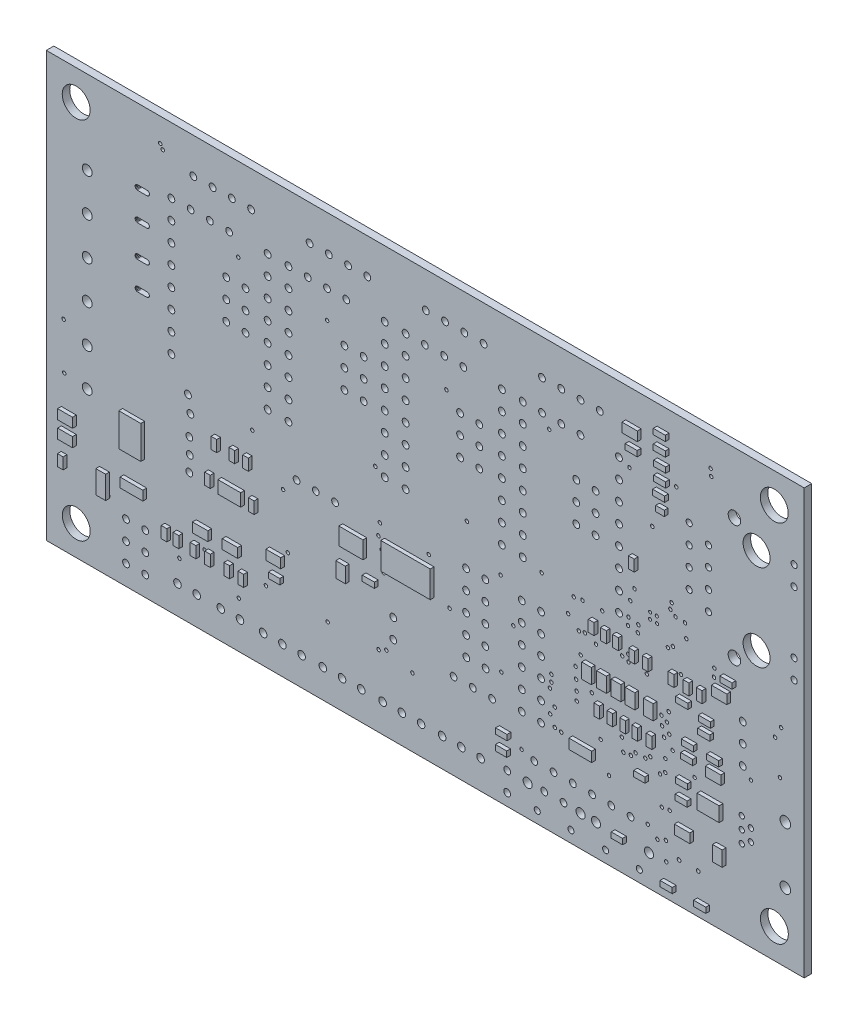
SolidWorks part; units mm, degrees
ref_plane "Front Plane" through (0, 0, 0) normal (0, 0, 1) x (1, 0, 0)
ref_plane "Top Plane" through (0, 0, 0) normal (0, 1, 0) x (1, 0, 0)
ref_plane "Right Plane" through (0, 0, 0) normal (1, 0, 0) x (0, 0, -1)
sketch "Sketch1" plane through (0, 0, 0) normal (0, 0, 1) x (1, 0, 0)
  line L0 (-23.2947, 26.1235) -> (-23.4059, 26.1039)
  line L1 (-23.4059, 26.1039) -> (-24.6559, 26.1039)
  line L2 (-24.6559, 26.1039) -> (-24.767, 26.1235)
  line L3 (-24.767, 26.1235) -> (-24.8648, 26.18)
  line L4 (-24.8648, 26.18) -> (-24.9373, 26.2664)
  line L5 (-24.9373, 26.2664) -> (-24.9759, 26.3725)
  line L6 (-24.9759, 26.3725) -> (-24.9759, 26.4854)
  line L7 (-24.9759, 26.4854) -> (-24.9373, 26.5914)
  line L8 (-24.9373, 26.5914) -> (-24.8648, 26.6779)
  line L9 (-24.8648, 26.6779) -> (-24.767, 26.7343)
  line L10 (-24.767, 26.7343) -> (-24.6559, 26.7539)
  line L11 (-24.6559, 26.7539) -> (-23.2947, 26.7343)
  line L12 (-23.2947, 26.7343) -> (-23.197, 26.6779)
  line L13 (-23.197, 26.6779) -> (-23.1244, 26.5914)
  line L14 (-23.1244, 26.5914) -> (-23.0858, 26.4854)
  line L15 (-23.0858, 26.4854) -> (-23.0858, 26.3725)
  line L16 (-23.0858, 26.3725) -> (-23.1244, 26.2664)
  line L17 (-23.1244, 26.2664) -> (-23.197, 26.18)
  line L18 (-23.197, 26.18) -> (-23.2947, 26.1235)
  line L19 (-23.2947, 29.8319) -> (-23.4059, 29.8123)
  line L20 (-23.4059, 29.8123) -> (-24.6559, 29.8123)
  line L21 (-24.6559, 29.8123) -> (-24.767, 29.8319)
  line L22 (-24.767, 29.8319) -> (-24.8648, 29.8884)
  line L23 (-24.8648, 29.8884) -> (-24.9373, 29.9748)
  line L24 (-24.9373, 29.9748) -> (-24.9759, 30.0809)
  line L25 (-24.9759, 30.0809) -> (-24.9759, 30.1938)
  line L26 (-24.9759, 30.1938) -> (-24.9373, 30.2998)
  line L27 (-24.9373, 30.2998) -> (-24.8648, 30.3863)
  line L28 (-24.8648, 30.3863) -> (-24.767, 30.4427)
  line L29 (-24.767, 30.4427) -> (-24.6559, 30.4623)
  line L30 (-24.6559, 30.4623) -> (-23.2947, 30.4427)
  line L31 (-23.2947, 30.4427) -> (-23.197, 30.3863)
  line L32 (-23.197, 30.3863) -> (-23.1244, 30.2998)
  line L33 (-23.1244, 30.2998) -> (-23.0858, 30.1938)
  line L34 (-23.0858, 30.1938) -> (-23.0858, 30.0809)
  line L35 (-23.0858, 30.0809) -> (-23.1244, 29.9748)
  line L36 (-23.1244, 29.9748) -> (-23.197, 29.8884)
  line L37 (-23.197, 29.8884) -> (-23.2947, 29.8319)
  line L38 (-23.2947, 34.0229) -> (-23.4059, 34.0033)
  line L39 (-23.4059, 34.0033) -> (-24.6559, 34.0033)
  line L40 (-24.6559, 34.0033) -> (-24.767, 34.0229)
  line L41 (-24.767, 34.0229) -> (-24.8648, 34.0794)
  line L42 (-24.8648, 34.0794) -> (-24.9373, 34.1658)
  line L43 (-24.9373, 34.1658) -> (-24.9759, 34.2719)
  line L44 (-24.9759, 34.2719) -> (-24.9759, 34.3848)
  line L45 (-24.9759, 34.3848) -> (-24.9373, 34.4908)
  line L46 (-24.9373, 34.4908) -> (-24.8648, 34.5773)
  line L47 (-24.8648, 34.5773) -> (-24.767, 34.6337)
  line L48 (-24.767, 34.6337) -> (-24.6559, 34.6533)
  line L49 (-24.6559, 34.6533) -> (-23.2947, 34.6337)
  line L50 (-23.2947, 34.6337) -> (-23.197, 34.5773)
  line L51 (-23.197, 34.5773) -> (-23.1244, 34.4908)
  line L52 (-23.1244, 34.4908) -> (-23.0858, 34.3848)
  line L53 (-23.0858, 34.3848) -> (-23.0858, 34.2719)
  line L54 (-23.0858, 34.2719) -> (-23.1244, 34.1658)
  line L55 (-23.1244, 34.1658) -> (-23.197, 34.0794)
  line L56 (-23.197, 34.0794) -> (-23.2947, 34.0229)
  line L57 (-23.2947, 37.7313) -> (-23.4059, 37.7117)
  line L58 (-23.4059, 37.7117) -> (-24.6559, 37.7117)
  line L59 (-24.6559, 37.7117) -> (-24.767, 37.7313)
  line L60 (-24.767, 37.7313) -> (-24.8648, 37.7878)
  line L61 (-24.8648, 37.7878) -> (-24.9373, 37.8742)
  line L62 (-24.9373, 37.8742) -> (-24.9759, 37.9803)
  line L63 (-24.9759, 37.9803) -> (-24.9759, 38.0932)
  line L64 (-24.9759, 38.0932) -> (-24.9373, 38.1992)
  line L65 (-24.9373, 38.1992) -> (-24.8648, 38.2857)
  line L66 (-24.8648, 38.2857) -> (-24.767, 38.3421)
  line L67 (-24.767, 38.3421) -> (-24.6559, 38.3617)
  line L68 (-24.6559, 38.3617) -> (-23.2947, 38.3421)
  line L69 (-23.2947, 38.3421) -> (-23.197, 38.2857)
  line L70 (-23.197, 38.2857) -> (-23.1244, 38.1992)
  line L71 (-23.1244, 38.1992) -> (-23.0858, 38.0932)
  line L72 (-23.0858, 38.0932) -> (-23.0858, 37.9803)
  line L73 (-23.0858, 37.9803) -> (-23.1244, 37.8742)
  line L74 (-23.1244, 37.8742) -> (-23.197, 37.7878)
  line L75 (-23.197, 37.7878) -> (-23.2947, 37.7313)
  line L76 (63.3071, -8.3113) -> (63.3071, 47.6887)
  line L77 (63.3071, 47.6887) -> (-36.6929, 47.6887)
  line L78 (-36.6929, 47.6887) -> (-36.6929, -8.3113)
  line L79 (-36.6929, -8.3113) -> (63.3071, -8.3113)
  circle A0 centre (16.5171, 10.5421) radius 0.2286
  circle A1 centre (16.1038, 35.2921) radius 0.2286
  circle A2 centre (23.2471, 17.7087) radius 0.2286
  circle A3 centre (28.655, 20.675) radius 0.2286
  circle A4 centre (33.2873, 8.324) radius 0.2286
  circle A5 centre (29.7584, 8.0388) radius 0.2286
  circle A6 centre (7.3249, 15.7176) radius 0.2286
  circle A7 centre (0.3571, 35.3487) radius 0.2286
  circle A8 centre (18.7985, 21.6213) radius 0.2286
  circle A9 centre (29.9537, 9.7164) radius 0.2286
  circle A10 centre (29.9571, 8.8187) radius 0.2286
  circle A11 centre (13.775, 15.3137) radius 0.2286
  circle A12 centre (-11.3662, 36.7154) radius 0.2286
  circle A13 centre (-9.5149, 17.8687) radius 0.2286
  circle A14 centre (31.2407, 3.7565) radius 0.2286
  circle A15 centre (23.3471, 6.6687) radius 0.2286
  circle A16 centre (-4.8229, 6.2254) radius 0.2286
  circle A17 centre (-5.4559, 13.1265) radius 0.2286
  circle A18 centre (44.2803, 5.4921) radius 0.2286
  circle A19 centre (44.978, 6.0054) radius 0.2286
  circle A20 centre (44.4754, 12.3113) radius 0.2286
  circle A21 centre (43.2671, 33.2787) radius 0.2286
  circle A22 centre (42.6598, -1.0665) radius 0.2286
  circle A23 centre (34.3671, 16.6587) radius 0.2286
  circle A24 centre (60.1092, 12.993) radius 0.2286
  circle A25 centre (34.0541, 20.2274) radius 0.2286
  circle A26 centre (32.8957, 20.0402) radius 0.2286
  circle A27 centre (59.4648, 17.2764) radius 0.2286
  circle A28 centre (35.8363, 16.1019) radius 0.2286
  circle A29 centre (45.058, -1.7073) radius 0.2286
  circle A30 centre (45.196, 11.8765) radius 0.2286
  circle A31 centre (45.4971, 10.6387) radius 0.2286
  circle A32 centre (47.5771, 24.4066) radius 0.2286
  circle A33 centre (45.9424, 9.0166) radius 0.2286
  circle A34 centre (7.1314, 14.1277) radius 0.2286
  circle A35 centre (8.1788, 1.5814) radius 0.2286
  circle A36 centre (7.1505, 1.1324) radius 0.2286
  circle A37 centre (7.5602, 12.7235) radius 0.2286
  circle A38 centre (33.5707, 16.4904) radius 0.2286
  circle A39 centre (30.4055, 3.869) radius 0.2286
  circle A40 centre (33.8171, 13.8587) radius 0.2286
  circle A41 centre (45.5541, 1.9605) radius 0.2286
  circle A42 centre (44.5228, 1.8236) radius 0.2286
  circle A43 centre (29.78, 5.116) radius 0.2286
  circle A44 centre (35.2805, 10.2754) radius 0.2286
  circle A45 centre (33.1373, 12.2162) radius 0.2286
  circle A46 centre (24.9359, 12.76) radius 0.2286
  circle A47 centre (44.9896, 7.609) radius 0.2286
  circle A48 centre (36.4471, 5.5187) radius 0.2286
  circle A49 centre (48.8405, 7.3754) radius 0.2286
  circle A50 centre (39.4484, 5.5491) radius 0.2286
  circle A51 centre (40.4371, 5.6921) radius 0.2286
  circle A52 centre (33.2744, 9.4587) radius 0.2286
  circle A53 centre (33.2072, 10.7806) radius 0.2286
  circle A54 centre (-19.1295, -1.5746) radius 0.2286
  circle A55 centre (45.4266, 13.1794) radius 0.2286
  circle A56 centre (11.6171, 0.7045) radius 0.2286
  circle A57 centre (41.4271, 21.1092) radius 0.2286
  circle A58 centre (47.7471, 22.6787) radius 0.2286
  circle A59 centre (40.9171, 24.9787) radius 0.2286
  circle A60 centre (41.361, 20.1656) radius 0.2286
  circle A61 centre (46.4271, 39.3687) radius 0.2286
  circle A62 centre (40.2556, 38.4838) radius 0.2286
  circle A63 centre (40.3571, 23.3387) radius 0.2286
  circle A64 centre (41.0541, 6.2989) radius 0.2286
  circle A65 centre (39.2531, 7.1827) radius 0.2286
  circle A66 centre (42.3388, 6.3287) radius 0.2286
  circle A67 centre (42.9945, 6.828) radius 0.2286
  circle A68 centre (30.3864, 6.1865) radius 0.2286
  circle A69 centre (-34.4069, 18.1115) radius 0.2286
  circle A70 centre (-28.5043, 0.9409) radius 0.2286
  circle A71 centre (26.0116, -0.8344) radius 0.2286
  circle A72 centre (7.8107, 10.2366) radius 0.2286
  circle A73 centre (29.6671, 37.5587) radius 0.2286
  circle A74 centre (45.6571, 24.9887) radius 0.2286
  circle A75 centre (46.3271, 24.4887) radius 0.2286
  circle A76 centre (45.8071, 25.8287) radius 0.2286
  circle A77 centre (40.0912, 17.0729) radius 0.2286
  circle A78 centre (40.1231, 16.2051) radius 0.2286
  circle A79 centre (40.1205, 21.3421) radius 0.2286
  circle A80 centre (47.0471, 18.2387) radius 0.2286
  circle A81 centre (51.4538, 21.1754) radius 0.2286
  circle A82 centre (40.0605, 20.3421) radius 0.2286
  circle A83 centre (36.6571, 20.3187) radius 0.2286
  circle A84 centre (45.3255, 20.4579) radius 0.2286
  circle A85 centre (39.2971, 16.4887) radius 0.2286
  circle A86 centre (45.9871, 20.9187) radius 0.2286
  circle A87 centre (42.5415, 16.037) radius 0.2286
  circle A88 centre (-11.2929, -2.2113) radius 0.2286
  circle A89 centre (32.1571, 17.7487) radius 0.2286
  circle A90 centre (-15.7962, 1.0487) radius 0.2286
  circle A91 centre (45.1071, -4.1313) radius 0.2286
  circle A92 centre (44.8148, 9.9587) radius 0.2286
  circle A93 centre (0.4297, 0.9345) radius 0.2286
  circle A94 centre (43.9401, -2.1493) radius 0.2286
  circle A95 centre (51.4038, 20.1054) radius 0.2286
  circle A96 centre (56.2838, 10.7887) radius 0.2286
  circle A97 centre (60.2524, 18.7787) radius 0.2286
  circle A98 centre (44.5511, 11.1298) radius 0.2286
  circle A99 centre (-7.7129, 1.0087) radius 0.2286
  circle A100 centre (6.7171, 21.8554) radius 0.2286
  circle A101 centre (37.5541, 1.9585) radius 0.2286
  circle A102 centre (51.046, 42.8634) radius 0.2286
  circle A103 centre (50.9547, 43.7429) radius 0.2286
  circle A104 centre (-21.327, 44.0122) radius 0.2286
  circle A105 centre (-21.6644, 44.556) radius 0.2286
  circle A106 centre (-34.3297, 12.0029) radius 0.2286
  circle A107 centre (-9.6695, 43.0214) radius 0.45
  circle A108 centre (-12.2095, 43.0214) radius 0.45
  circle A109 centre (-14.7495, 43.0167) radius 0.45
  circle A110 centre (-17.2895, 43.0121) radius 0.45
  circle A111 centre (5.6671, 43.0314) radius 0.45
  circle A112 centre (3.1271, 43.0314) radius 0.45
  circle A113 centre (0.5871, 43.0267) radius 0.45
  circle A114 centre (-1.9529, 43.0221) radius 0.45
  circle A115 centre (21.0038, 43.0214) radius 0.45
  circle A116 centre (18.4638, 43.0214) radius 0.45
  circle A117 centre (15.9238, 43.0167) radius 0.45
  circle A118 centre (13.3838, 43.0121) radius 0.45
  circle A119 centre (36.3338, 43.0014) radius 0.45
  circle A120 centre (33.7938, 43.0014) radius 0.45
  circle A121 centre (31.2538, 42.9967) radius 0.45
  circle A122 centre (28.7138, 42.9921) radius 0.45
  circle A123 centre (42.9771, 22.5087) radius 0.2032
  circle A124 centre (43.8889, 22.474) radius 0.2032
  circle A125 centre (43.8541, 23.3249) radius 0.2032
  circle A126 centre (42.9858, 23.3249) radius 0.2032
  circle A127 centre (32.5312, -6.7873) radius 0.4
  circle A128 centre (28.0862, -6.7873) radius 0.4
  circle A129 centre (33.8012, -4.2473) radius 0.6
  circle A130 centre (26.8162, -4.2473) radius 0.6
  circle A131 centre (57.0241, 37.3877) radius 1.778
  circle A132 centre (57.0241, 25.9577) radius 1.778
  circle A133 centre (61.9771, 35.7367) radius 0.4064
  circle A134 centre (61.9771, 38.2767) radius 0.4064
  circle A135 centre (48.1341, 28.4977) radius 0.4064
  circle A136 centre (50.6741, 27.2277) radius 0.4064
  circle A137 centre (54.1031, 23.6717) radius 0.8255
  circle A138 centre (54.1031, 39.6737) radius 0.8255
  circle A139 centre (48.1341, 33.5777) radius 0.4064
  circle A140 centre (50.6741, 29.7677) radius 0.4064
  circle A141 centre (50.6741, 32.3077) radius 0.4064
  circle A142 centre (48.1341, 31.0377) radius 0.4064
  circle A143 centre (50.6741, 34.8477) radius 0.4064
  circle A144 centre (48.1341, 36.1177) radius 0.4064
  circle A145 centre (61.9771, 27.6087) radius 0.4064
  circle A146 centre (61.9771, 25.0687) radius 0.4064
  circle A147 centre (9.0886, 3.245) radius 0.4445
  circle A148 centre (9.0886, 5.785) radius 0.4445
  circle A149 centre (21.2699, 6.0397) radius 0.4445
  circle A150 centre (18.7299, 6.0397) radius 0.4445
  circle A151 centre (41.5524, -6.7788) radius 0.4
  circle A152 centre (37.1074, -6.7788) radius 0.4
  circle A153 centre (42.8224, -4.2388) radius 0.6
  circle A154 centre (35.8374, -4.2388) radius 0.6
  circle A155 centre (59.3696, -4.3808) radius 1.8415
  circle A156 centre (59.3604, 43.7422) radius 1.8415
  circle A157 centre (-32.7488, 43.7345) radius 1.8415
  circle A158 centre (-32.7404, -4.3748) radius 1.8415
  circle A159 centre (-17.8195, 12.9654) radius 0.45
  circle A160 centre (-17.8184, 8.8932) radius 0.45
  circle A161 centre (-17.7629, 10.9287) radius 0.45
  circle A162 centre (-17.6821, 15.653) radius 0.45
  circle A163 centre (-18.0029, 17.7187) radius 0.45
  circle A164 centre (33.7912, 38.9854) radius 0.4445
  circle A165 centre (31.2512, 38.9854) radius 0.4445
  circle A166 centre (28.7112, 38.9854) radius 0.4445
  circle A167 centre (26.1712, 21.2054) radius 0.45
  circle A168 centre (26.1712, 36.4454) radius 0.45
  circle A169 centre (38.8712, 36.4454) radius 0.45
  circle A170 centre (38.8712, 33.9054) radius 0.45
  circle A171 centre (38.8712, 31.3654) radius 0.45
  circle A172 centre (38.8712, 28.8254) radius 0.45
  circle A173 centre (38.8712, 26.2854) radius 0.45
  circle A174 centre (38.8712, 23.7454) radius 0.45
  circle A175 centre (26.1712, 23.7454) radius 0.45
  circle A176 centre (26.1712, 38.9854) radius 0.45
  circle A177 centre (38.8712, 21.2054) radius 0.45
  circle A178 centre (38.8712, 38.9854) radius 0.45
  circle A179 centre (26.1712, 26.2854) radius 0.45
  circle A180 centre (26.1712, 28.8254) radius 0.45
  circle A181 centre (26.1712, 33.9054) radius 0.45
  circle A182 centre (26.1712, 31.3654) radius 0.45
  circle A183 centre (18.3371, 39.0254) radius 0.4445
  circle A184 centre (15.7971, 39.0254) radius 0.4445
  circle A185 centre (13.2571, 39.0254) radius 0.4445
  circle A186 centre (10.7171, 21.2454) radius 0.45
  circle A187 centre (10.7171, 36.4854) radius 0.45
  circle A188 centre (23.4171, 36.4854) radius 0.45
  circle A189 centre (23.4171, 33.9454) radius 0.45
  circle A190 centre (23.4171, 31.4054) radius 0.45
  circle A191 centre (23.4171, 28.8654) radius 0.45
  circle A192 centre (23.4171, 26.3254) radius 0.45
  circle A193 centre (23.4171, 23.7854) radius 0.45
  circle A194 centre (10.7171, 23.7854) radius 0.45
  circle A195 centre (10.7171, 39.0254) radius 0.45
  circle A196 centre (23.4171, 21.2454) radius 0.45
  circle A197 centre (23.4171, 39.0254) radius 0.45
  circle A198 centre (10.7171, 26.3254) radius 0.45
  circle A199 centre (10.7171, 28.8654) radius 0.45
  circle A200 centre (10.7171, 33.9454) radius 0.45
  circle A201 centre (10.7171, 31.4054) radius 0.45
  circle A202 centre (2.8838, 39.0154) radius 0.4445
  circle A203 centre (0.3438, 39.0154) radius 0.4445
  circle A204 centre (-2.1962, 39.0154) radius 0.4445
  circle A205 centre (-4.7362, 21.2354) radius 0.45
  circle A206 centre (-4.7362, 36.4754) radius 0.45
  circle A207 centre (7.9638, 36.4754) radius 0.45
  circle A208 centre (7.9638, 33.9354) radius 0.45
  circle A209 centre (7.9638, 31.3954) radius 0.45
  circle A210 centre (7.9638, 28.8554) radius 0.45
  circle A211 centre (7.9638, 26.3154) radius 0.45
  circle A212 centre (7.9638, 23.7754) radius 0.45
  circle A213 centre (-4.7362, 23.7754) radius 0.45
  circle A214 centre (-4.7362, 39.0154) radius 0.45
  circle A215 centre (7.9638, 21.2354) radius 0.45
  circle A216 centre (7.9638, 39.0154) radius 0.45
  circle A217 centre (-4.7362, 26.3154) radius 0.45
  circle A218 centre (-4.7362, 28.8554) radius 0.45
  circle A219 centre (-4.7362, 33.9354) radius 0.45
  circle A220 centre (-4.7362, 31.3954) radius 0.45
  circle A221 centre (-12.5695, 39.0254) radius 0.4445
  circle A222 centre (-15.1095, 39.0254) radius 0.4445
  circle A223 centre (-17.6495, 39.0254) radius 0.4445
  circle A224 centre (-20.1895, 21.2454) radius 0.45
  circle A225 centre (-20.1895, 36.4854) radius 0.45
  circle A226 centre (-7.4895, 36.4854) radius 0.45
  circle A227 centre (-7.4895, 33.9454) radius 0.45
  circle A228 centre (-7.4895, 31.4054) radius 0.45
  circle A229 centre (-7.4895, 28.8654) radius 0.45
  circle A230 centre (-7.4895, 26.3254) radius 0.45
  circle A231 centre (-7.4895, 23.7854) radius 0.45
  circle A232 centre (-20.1895, 23.7854) radius 0.45
  circle A233 centre (-20.1895, 39.0254) radius 0.45
  circle A234 centre (-7.4895, 21.2454) radius 0.45
  circle A235 centre (-7.4895, 39.0254) radius 0.45
  circle A236 centre (-20.1895, 26.3254) radius 0.45
  circle A237 centre (-20.1895, 28.8654) radius 0.45
  circle A238 centre (-20.1895, 33.9454) radius 0.45
  circle A239 centre (-20.1895, 31.4054) radius 0.45
  circle A240 centre (55.1971, 16.9454) radius 0.4445
  circle A241 centre (55.1971, 14.4054) radius 0.4445
  circle A242 centre (55.1971, 11.8654) radius 0.4445
  circle A243 centre (-13.6768, -4.5792) radius 0.5
  circle A244 centre (-11.1368, -4.5745) radius 0.5
  circle A245 centre (-19.3847, -4.5792) radius 0.5
  circle A246 centre (-16.8447, -4.5745) radius 0.5
  circle A247 centre (-3.6729, 15.0986) radius 0.4445
  circle A248 centre (-1.1329, 15.0986) radius 0.4445
  circle A249 centre (1.4071, 15.0986) radius 0.4445
  circle A250 centre (22.1258, 3.0017) radius 0.4445
  circle A251 centre (19.5858, 3.0017) radius 0.4445
  circle A252 centre (17.0458, 3.0017) radius 0.4445
  circle A253 centre (15.5317, -4.5494) radius 0.5
  circle A254 centre (18.0717, -4.5448) radius 0.5
  circle A255 centre (20.6117, -4.5401) radius 0.5
  circle A256 centre (7.6781, -4.5494) radius 0.5
  circle A257 centre (10.2181, -4.5448) radius 0.5
  circle A258 centre (12.7581, -4.5401) radius 0.5
  circle A259 centre (-0.2119, -4.5494) radius 0.5
  circle A260 centre (2.3281, -4.5448) radius 0.5
  circle A261 centre (4.8681, -4.5401) radius 0.5
  circle A262 centre (-8.0837, -4.5858) radius 0.5
  circle A263 centre (-5.5437, -4.5812) radius 0.5
  circle A264 centre (-3.0037, -4.5765) radius 0.5
  circle A265 centre (-12.9462, 28.5621) radius 0.4445
  circle A266 centre (-12.9462, 31.1021) radius 0.4445
  circle A267 centre (-12.9462, 33.6421) radius 0.4445
  circle A268 centre (-10.4062, 28.5621) radius 0.4445
  circle A269 centre (-10.4062, 31.1021) radius 0.4445
  circle A270 centre (-10.4062, 33.6421) radius 0.4445
  circle A271 centre (2.6405, 28.5454) radius 0.4445
  circle A272 centre (2.6405, 31.0854) radius 0.4445
  circle A273 centre (2.6405, 33.6254) radius 0.4445
  circle A274 centre (5.1805, 28.5454) radius 0.4445
  circle A275 centre (5.1805, 31.0854) radius 0.4445
  circle A276 centre (5.1805, 33.6254) radius 0.4445
  circle A277 centre (17.8997, 28.4679) radius 0.4445
  circle A278 centre (17.8997, 31.0079) radius 0.4445
  circle A279 centre (17.8997, 33.5479) radius 0.4445
  circle A280 centre (20.4397, 28.4679) radius 0.4445
  circle A281 centre (20.4397, 31.0079) radius 0.4445
  circle A282 centre (20.4397, 33.5479) radius 0.4445
  circle A283 centre (33.2389, 28.5087) radius 0.4445
  circle A284 centre (33.2389, 31.0487) radius 0.4445
  circle A285 centre (33.2389, 33.5887) radius 0.4445
  circle A286 centre (35.7789, 28.5087) radius 0.4445
  circle A287 centre (35.7789, 31.0487) radius 0.4445
  circle A288 centre (35.7789, 33.5887) radius 0.4445
  circle A289 centre (24.1205, -6.7339) radius 0.4445
  circle A290 centre (24.1205, -4.1939) radius 0.4445
  circle A291 centre (27.6961, -1.3263) radius 0.4445
  circle A292 centre (30.2361, -1.3263) radius 0.4445
  circle A293 centre (32.7761, -1.3263) radius 0.4445
  circle A294 centre (35.3161, -1.3263) radius 0.4445
  circle A295 centre (37.8561, -1.3263) radius 0.4445
  circle A296 centre (40.3961, -1.3263) radius 0.4445
  circle A297 centre (-31.2929, 11.6887) radius 0.65
  circle A298 centre (-31.2929, 16.6887) radius 0.65
  circle A299 centre (-31.2929, 21.6887) radius 0.65
  circle A300 centre (-31.2929, 26.6887) radius 0.65
  circle A301 centre (-31.2929, 31.6887) radius 0.65
  circle A302 centre (-31.2929, 36.6887) radius 0.65
  circle A303 centre (60.8153, 8.2611) radius 0.7
  circle A304 centre (60.8153, 0.7564) radius 0.7
  circle A305 centre (56.2671, 5.3087) radius 0.35
  circle A306 centre (56.2671, 3.7087) radius 0.35
  circle A307 centre (55.0671, 6.1087) radius 0.35
  circle A308 centre (55.0671, 2.9087) radius 0.35
  circle A309 centre (55.0671, 4.5087) radius 0.35
  circle A310 centre (28.5851, 16.1997) radius 0.4445
  circle A311 centre (28.5851, 13.6597) radius 0.4445
  circle A312 centre (28.5851, 11.1197) radius 0.4445
  circle A313 centre (26.0451, 16.1997) radius 0.4445
  circle A314 centre (26.0451, 13.6597) radius 0.4445
  circle A315 centre (26.0451, 11.1197) radius 0.4445
  circle A316 centre (-23.6384, -0.6061) radius 0.4445
  circle A317 centre (-23.6384, -3.1461) radius 0.4445
  circle A318 centre (-23.6384, -5.6861) radius 0.4445
  circle A319 centre (-26.1784, -0.6061) radius 0.4445
  circle A320 centre (-26.1784, -3.1461) radius 0.4445
  circle A321 centre (-26.1784, -5.6861) radius 0.4445
  circle A322 centre (28.5851, 8.5797) radius 0.4445
  circle A323 centre (28.5851, 6.0397) radius 0.4445
  circle A324 centre (28.5851, 3.4997) radius 0.4445
  circle A325 centre (26.0451, 8.5797) radius 0.4445
  circle A326 centre (26.0451, 6.0397) radius 0.4445
  circle A327 centre (26.0451, 3.4997) radius 0.4445
  circle A328 centre (18.6949, 11.1179) radius 0.4445
  circle A329 centre (18.6949, 13.6579) radius 0.4445
  circle A330 centre (18.6949, 16.1979) radius 0.4445
  circle A331 centre (21.2349, 11.1179) radius 0.4445
  circle A332 centre (21.2349, 13.6579) radius 0.4445
  circle A333 centre (21.2349, 16.1979) radius 0.4445
  circle A334 centre (21.2349, 8.5779) radius 0.4445
  circle A335 centre (18.6949, 8.5779) radius 0.4445
  circle A336 centre (31.5511, -4.1456) radius 0.4445
  circle A337 centre (29.0111, -4.1456) radius 0.4445
  circle A338 centre (46.796, -3.0784) radius 0.25
  circle A339 centre (49.3193, -3.0803) radius 0.25
extrude "Boss-Extrude1" add sketch "Sketch1" against normal blind 0.991
sketch "Sketch2" plane through (0, 0, 0) normal (0, 0, 1) x (1, 0, 0)
  line L0 (-32.7488, 43.7345) -> (59.3696, -4.3808) construction
  line L1 (-32.7404, -4.3748) -> (59.3604, 43.7422) construction
  line L2 (-24.0309, 26.1039) -> (-23.9753, 30.4525) construction
  line L3 (-24.6559, 26.1039) -> (-23.4059, 26.1039) construction
  line L4 (-23.2947, 30.4427) -> (-24.6559, 30.4623) construction
  line L5 (-24.0309, 34.0033) -> (-23.9753, 38.3519) construction
  line L6 (-24.6559, 34.0033) -> (-23.4059, 34.0033) construction
  line L7 (-23.2947, 38.3421) -> (-24.6559, 38.3617) construction
  point P8 (13.3104, 19.6769)
sketch "Sketch3" plane through (0, 0, -0.991) normal (0, 0, -1) x (-1, 0, 0)
  line L0 (36.6929, -8.3113) -> (-63.3071, -8.3113) construction
  line L1 (-32.5371, 3.9387) -> (-46.5671, 3.9387)
  line L2 (-32.5371, 3.9387) -> (-32.5371, 17.9687)
  line L3 (-32.5371, 17.9687) -> (-46.5671, 17.9687)
  line L4 (-46.5671, 3.9387) -> (-46.5671, 17.9687)
  line L5 (-63.3071, -8.3113) -> (-63.3071, 47.6887) construction
  dimension "D1" = 12.25
  dimension "D2" = 16.74
  dimension "D3" = 14.03
extrude "Boss-Extrude2" add sketch "Sketch3" along normal blind 1.61
chamfer "Chamfer1" distance 0.61 angle 45 4 edges at (32.5371, 3.9387, -1.796) (32.5371, 17.9687, -1.796) (46.5671, 17.9687, -1.796) (46.5671, 3.9387, -1.796)
chamfer "Chamfer2" distance 0.61 angle 45 8 edges at (46.2621, 4.2437, -2.601) (46.5671, 10.9537, -2.601) (46.2621, 17.6637, -2.601) (39.5521, 17.9687, -2.601) (32.8421, 17.6637, -2.601) (32.5371, 10.9537, -2.601) (32.8421, 4.2437, -2.601) (39.5521, 3.9387, -2.601)
sketch "Sketch4" plane through (0, 0, 0) normal (0, 0, 1) x (1, 0, 0)
  line B0 (-36.6929, 47.6887) -> (-36.6929, -8.3113) construction
  line B1 (-36.6929, -8.3113) -> (63.3071, -8.3113) construction
  line B2 (63.3071, 47.6887) -> (-36.6929, 47.6887) construction
  line B3 (63.3071, -8.3113) -> (63.3071, 47.6887) construction
  line B4 (-29.6656, 3.6663) -> (-28.3606, 3.6663)
  line B5 (-28.3606, 3.6663) -> (-28.3606, 0.6544)
  line B6 (-28.3606, 0.6544) -> (-29.6656, 0.6544)
  line B7 (-29.6656, 0.6544) -> (-29.6656, 3.6663)
  line B8 (-34.7169, 1.3554) -> (-33.9692, 1.3554)
  line B9 (-33.9692, 1.3554) -> (-33.9692, 2.8489)
  line B10 (-33.9692, 2.8489) -> (-34.7169, 2.8489)
  line B11 (-34.7169, 2.8489) -> (-34.7169, 1.3554)
  line B12 (-34.7033, 4.5002) -> (-32.7358, 4.5002)
  line B13 (-32.7358, 4.5002) -> (-32.7358, 5.7752)
  line B14 (-32.7358, 5.7752) -> (-34.7033, 5.7752)
  line B15 (-34.7033, 5.7752) -> (-34.7033, 4.5002)
  line B16 (-34.7033, 6.7189) -> (-32.7358, 6.7189)
  line B17 (-32.7358, 6.7189) -> (-32.7358, 7.9939)
  line B18 (-32.7358, 7.9939) -> (-34.7033, 7.9939)
  line B19 (-34.7033, 7.9939) -> (-34.7033, 6.7189)
  line B20 (-26.465, 3.0514) -> (-23.4532, 3.0514)
  line B21 (-23.4532, 3.0514) -> (-23.4532, 4.2981)
  line B22 (-23.4532, 4.2981) -> (-26.465, 4.2981)
  line B23 (-26.465, 4.2981) -> (-26.465, 3.0514)
  line B24 (-21.0347, -0.0306) -> (-20.287, -0.0306)
  line B25 (-20.287, -0.0306) -> (-20.287, 1.4811)
  line B26 (-20.287, 1.4811) -> (-21.0347, 1.4811)
  line B27 (-21.0347, 1.4811) -> (-21.0347, -0.0306)
  line B28 (-19.462, -0.0273) -> (-18.7144, -0.0273)
  line B29 (-18.7144, -0.0273) -> (-18.7144, 1.4845)
  line B30 (-18.7144, 1.4845) -> (-19.462, 1.4845)
  line B31 (-19.462, 1.4845) -> (-19.462, -0.0273)
  line B32 (-17.2087, -0.0539) -> (-16.461, -0.0539)
  line B33 (-16.461, -0.0539) -> (-16.461, 1.4578)
  line B34 (-16.461, 1.4578) -> (-17.2087, 1.4578)
  line B35 (-17.2087, 1.4578) -> (-17.2087, -0.0539)
  line B36 (-15.3047, -0.0887) -> (-14.557, -0.0887)
  line B37 (-14.557, -0.0887) -> (-14.557, 1.423)
  line B38 (-14.557, 1.423) -> (-15.3047, 1.423)
  line B39 (-15.3047, 1.423) -> (-15.3047, -0.0887)
  line B40 (-12.7587, -0.1173) -> (-12.011, -0.1173)
  line B41 (-12.011, -0.1173) -> (-12.011, 1.3945)
  line B42 (-12.011, 1.3945) -> (-12.7587, 1.3945)
  line B43 (-12.7587, 1.3945) -> (-12.7587, -0.1173)
  line B44 (-10.9054, -0.1821) -> (-10.1577, -0.1821)
  line B45 (-10.1577, -0.1821) -> (-10.1577, 1.3297)
  line B46 (-10.1577, 1.3297) -> (-10.9054, 1.3297)
  line B47 (-10.9054, 1.3297) -> (-10.9054, -0.1821)
  line B48 (-15.308, 8.932) -> (-14.5604, 8.932)
  line B49 (-14.5604, 8.932) -> (-14.5604, 10.4437)
  line B50 (-14.5604, 10.4437) -> (-15.308, 10.4437)
  line B51 (-15.308, 10.4437) -> (-15.308, 8.932)
  line B52 (-14.458, 13.4458) -> (-13.7104, 13.4458)
  line B53 (-13.7104, 13.4458) -> (-13.7104, 14.9575)
  line B54 (-13.7104, 14.9575) -> (-14.458, 14.9575)
  line B55 (-14.458, 14.9575) -> (-14.458, 13.4458)
  line B56 (-12.0847, 13.3663) -> (-11.337, 13.3663)
  line B57 (-11.337, 13.3663) -> (-11.337, 14.8781)
  line B58 (-11.337, 14.8781) -> (-12.0847, 14.8781)
  line B59 (-12.0847, 14.8781) -> (-12.0847, 13.3663)
  line B60 (-10.2854, 13.4111) -> (-9.5377, 13.4111)
  line B61 (-9.5377, 13.4111) -> (-9.5377, 14.9229)
  line B62 (-9.5377, 14.9229) -> (-10.2854, 14.9229)
  line B63 (-10.2854, 14.9229) -> (-10.2854, 13.4111)
  line B64 (36.0513, 8.2411) -> (36.799, 8.2411)
  line B65 (36.799, 8.2411) -> (36.799, 9.7529)
  line B66 (36.799, 9.7529) -> (36.0513, 9.7529)
  line B67 (36.0513, 9.7529) -> (36.0513, 8.2411)
  line B68 (37.7825, 8.2395) -> (38.5301, 8.2395)
  line B69 (38.5301, 8.2395) -> (38.5301, 9.7513)
  line B70 (38.5301, 9.7513) -> (37.7825, 9.7513)
  line B71 (37.7825, 9.7513) -> (37.7825, 8.2395)
  line B72 (39.4746, 8.2627) -> (40.2223, 8.2627)
  line B73 (40.2223, 8.2627) -> (40.2223, 9.7745)
  line B74 (40.2223, 9.7745) -> (39.4746, 9.7745)
  line B75 (39.4746, 9.7745) -> (39.4746, 8.2627)
  line B76 (41.0758, 8.2345) -> (41.8235, 8.2345)
  line B77 (41.8235, 8.2345) -> (41.8235, 9.7462)
  line B78 (41.8235, 9.7462) -> (41.0758, 9.7462)
  line B79 (41.0758, 9.7462) -> (41.0758, 8.2345)
  line B80 (35.3119, 18.9297) -> (36.0769, 18.9297)
  line B81 (36.0769, 18.9297) -> (36.0769, 17.4362)
  line B82 (36.0769, 17.4362) -> (35.3119, 17.4362)
  line B83 (35.3119, 17.4362) -> (35.3119, 18.9297)
  line B84 (36.9268, 18.8025) -> (37.6918, 18.8025)
  line B85 (37.6918, 18.8025) -> (37.6918, 17.3091)
  line B86 (37.6918, 17.3091) -> (36.9268, 17.3091)
  line B87 (36.9268, 17.3091) -> (36.9268, 18.8025)
  line B88 (38.5268, 18.8125) -> (39.2918, 18.8125)
  line B89 (39.2918, 18.8125) -> (39.2918, 17.3191)
  line B90 (39.2918, 17.3191) -> (38.5268, 17.3191)
  line B91 (38.5268, 17.3191) -> (38.5268, 18.8125)
  line B92 (40.6746, 18.3551) -> (41.4396, 18.3551)
  line B93 (41.4396, 18.3551) -> (41.4396, 16.8616)
  line B94 (41.4396, 16.8616) -> (40.6746, 16.8616)
  line B95 (40.6746, 16.8616) -> (40.6746, 18.3551)
  line B96 (42.4546, 18.3651) -> (43.2196, 18.3651)
  line B97 (43.2196, 18.3651) -> (43.2196, 16.8716)
  line B98 (43.2196, 16.8716) -> (42.4546, 16.8716)
  line B99 (42.4546, 16.8716) -> (42.4546, 18.3651)
  line B100 (40.6168, 28.8454) -> (41.3818, 28.8454)
  line B101 (41.3818, 28.8454) -> (41.3818, 27.3519)
  line B102 (41.3818, 27.3519) -> (40.6168, 27.3519)
  line B103 (40.6168, 27.3519) -> (40.6168, 28.8454)
  line B104 (45.8568, 18.2668) -> (46.6218, 18.2668)
  line B105 (46.6218, 18.2668) -> (46.6218, 16.7733)
  line B106 (46.6218, 16.7733) -> (45.8568, 16.7733)
  line B107 (45.8568, 16.7733) -> (45.8568, 18.2668)
  line B108 (47.8318, 18.2968) -> (48.5968, 18.2968)
  line B109 (48.5968, 18.2968) -> (48.5968, 16.8033)
  line B110 (48.5968, 16.8033) -> (47.8318, 16.8033)
  line B111 (47.8318, 16.8033) -> (47.8318, 18.2968)
  line B112 (49.5646, 18.2751) -> (50.3296, 18.2751)
  line B113 (50.3296, 18.2751) -> (50.3296, 16.7816)
  line B114 (50.3296, 16.7816) -> (49.5646, 16.7816)
  line B115 (49.5646, 16.7816) -> (49.5646, 18.2751)
  line B116 (-16.9162, 2.6968) -> (-14.8762, 2.6968)
  line B117 (-14.8762, 2.6968) -> (-14.8762, 3.9433)
  line B118 (-14.8762, 3.9433) -> (-16.9162, 3.9433)
  line B119 (-16.9162, 3.9433) -> (-16.9162, 2.6968)
  line B120 (-12.9795, 2.7523) -> (-10.9395, 2.7523)
  line B121 (-10.9395, 2.7523) -> (-10.9395, 3.9988)
  line B122 (-10.9395, 3.9988) -> (-12.9795, 3.9988)
  line B123 (-12.9795, 3.9988) -> (-12.9795, 2.7523)
  line B124 (-7.2266, 4.4012) -> (-5.2591, 4.4012)
  line B125 (-5.2591, 4.4012) -> (-5.2591, 5.6762)
  line B126 (-5.2591, 5.6762) -> (-7.2266, 5.6762)
  line B127 (-7.2266, 5.6762) -> (-7.2266, 4.4012)
  line B128 (-6.8789, 2.4936) -> (-5.3854, 2.4936)
  line B129 (-5.3854, 2.4936) -> (-5.3854, 3.2412)
  line B130 (-5.3854, 3.2412) -> (-6.8789, 3.2412)
  line B131 (-6.8789, 3.2412) -> (-6.8789, 2.4936)
  line B132 (1.9996, 6.9597) -> (3.2746, 6.9597)
  line B133 (3.2746, 6.9597) -> (3.2746, 8.9754)
  line B134 (3.2746, 8.9754) -> (1.9996, 8.9754)
  line B135 (1.9996, 8.9754) -> (1.9996, 6.9597)
  line B136 (5.4915, 8.3437) -> (7.0979, 8.3437)
  line B137 (7.0979, 8.3437) -> (7.0979, 9.0697)
  line B138 (7.0979, 9.0697) -> (5.4915, 9.0697)
  line B139 (5.4915, 9.0697) -> (5.4915, 8.3437)
  line B140 (2.4071, 10.8587) -> (5.5871, 10.8587)
  line B141 (5.5871, 10.8587) -> (5.5871, 13.1387)
  line B142 (5.5871, 13.1387) -> (2.4071, 13.1387)
  line B143 (2.4071, 13.1387) -> (2.4071, 10.8587)
  line B144 (7.9372, 10.7364) -> (14.4652, 10.7364)
  line B145 (14.4652, 10.7364) -> (14.4652, 14.255)
  line B146 (14.4652, 14.255) -> (7.9372, 14.255)
  line B147 (7.9372, 14.255) -> (7.9372, 10.7364)
  line B148 (23.0652, -2.2433) -> (24.5587, -2.2433)
  line B149 (24.5587, -2.2433) -> (24.5587, -1.4956)
  line B150 (24.5587, -1.4956) -> (23.0652, -1.4956)
  line B151 (23.0652, -1.4956) -> (23.0652, -2.2433)
  line B152 (23.085, -0.3149) -> (24.5968, -0.3149)
  line B153 (24.5968, -0.3149) -> (24.5968, 0.4132)
  line B154 (24.5968, 0.4132) -> (23.085, 0.4132)
  line B155 (23.085, 0.4132) -> (23.085, -0.3149)
  line B156 (43.8903, 45.0417) -> (45.4777, 45.0417)
  line B157 (45.4777, 45.0417) -> (45.4777, 44.3136)
  line B158 (45.4777, 44.3136) -> (43.8903, 44.3136)
  line B159 (43.8903, 44.3136) -> (43.8903, 45.0417)
  line B160 (43.8903, 43.2539) -> (45.4777, 43.2539)
  line B161 (45.4777, 43.2539) -> (45.4777, 42.5257)
  line B162 (45.4777, 42.5257) -> (43.8903, 42.5257)
  line B163 (43.8903, 42.5257) -> (43.8903, 43.2539)
  line B164 (43.94, 41.4417) -> (45.5273, 41.4417)
  line B165 (45.5273, 41.4417) -> (45.5273, 40.7136)
  line B166 (45.5273, 40.7136) -> (43.94, 40.7136)
  line B167 (43.94, 40.7136) -> (43.94, 41.4417)
  line B168 (43.93, 39.7317) -> (45.5173, 39.7317)
  line B169 (45.5173, 39.7317) -> (45.5173, 39.0036)
  line B170 (45.5173, 39.0036) -> (43.93, 39.0036)
  line B171 (43.93, 39.0036) -> (43.93, 39.7317)
  line B172 (43.8003, 38.0439) -> (45.3877, 38.0439)
  line B173 (45.3877, 38.0439) -> (45.3877, 37.3157)
  line B174 (45.3877, 37.3157) -> (43.8003, 37.3157)
  line B175 (43.8003, 37.3157) -> (43.8003, 38.0439)
  line B176 (40.1866, 41.4451) -> (41.7739, 41.4451)
  line B177 (41.7739, 41.4451) -> (41.7739, 40.7169)
  line B178 (41.7739, 40.7169) -> (40.1866, 40.7169)
  line B179 (40.1866, 40.7169) -> (40.1866, 41.4451)
  line B180 (46.7795, 4.6939) -> (48.3669, 4.6939)
  line B181 (48.3669, 4.6939) -> (48.3669, 3.9657)
  line B182 (48.3669, 3.9657) -> (46.7795, 3.9657)
  line B183 (46.7795, 3.9657) -> (46.7795, 4.6939)
  line B184 (46.8081, 6.6708) -> (48.3954, 6.6708)
  line B185 (48.3954, 6.6708) -> (48.3954, 5.9426)
  line B186 (48.3954, 5.9426) -> (46.8081, 5.9426)
  line B187 (46.8081, 5.9426) -> (46.8081, 6.6708)
  line B188 (47.5125, 9.8139) -> (49.0999, 9.8139)
  line B189 (49.0999, 9.8139) -> (49.0999, 9.0857)
  line B190 (49.0999, 9.0857) -> (47.5125, 9.0857)
  line B191 (47.5125, 9.0857) -> (47.5125, 9.8139)
  line B192 (47.5859, 11.4072) -> (49.1732, 11.4072)
  line B193 (49.1732, 11.4072) -> (49.1732, 10.6791)
  line B194 (49.1732, 10.6791) -> (47.5859, 10.6791)
  line B195 (47.5859, 10.6791) -> (47.5859, 11.4072)
  line B196 (49.7595, 13.7239) -> (51.3469, 13.7239)
  line B197 (51.3469, 13.7239) -> (51.3469, 12.9957)
  line B198 (51.3469, 12.9957) -> (49.7595, 12.9957)
  line B199 (49.7595, 12.9957) -> (49.7595, 13.7239)
  line B200 (49.8395, 15.2539) -> (51.4269, 15.2539)
  line B201 (51.4269, 15.2539) -> (51.4269, 14.5257)
  line B202 (51.4269, 14.5257) -> (49.8395, 14.5257)
  line B203 (49.8395, 14.5257) -> (49.8395, 15.2539)
  line B204 (50.9329, 11.3739) -> (52.5202, 11.3739)
  line B205 (52.5202, 11.3739) -> (52.5202, 10.6457)
  line B206 (52.5202, 10.6457) -> (50.9329, 10.6457)
  line B207 (50.9329, 10.6457) -> (50.9329, 11.3739)
  line B208 (50.7639, 8.667) -> (52.8039, 8.667)
  line B209 (52.8039, 8.667) -> (52.8039, 9.8892)
  line B210 (52.8039, 9.8892) -> (50.7639, 9.8892)
  line B211 (50.7639, 9.8892) -> (50.7639, 8.667)
  line B212 (46.6705, -0.0096) -> (48.7105, -0.0096)
  line B213 (48.7105, -0.0096) -> (48.7105, 1.2125)
  line B214 (48.7105, 1.2125) -> (46.6705, 1.2125)
  line B215 (46.6705, 1.2125) -> (46.6705, -0.0096)
  line B216 (51.5605, 18.3104) -> (53.6005, 18.3104)
  line B217 (53.6005, 18.3104) -> (53.6005, 19.5325)
  line B218 (53.6005, 19.5325) -> (51.5605, 19.5325)
  line B219 (51.5605, 19.5325) -> (51.5605, 18.3104)
  line B220 (39.7538, 42.465) -> (41.7938, 42.465)
  line B221 (41.7938, 42.465) -> (41.7938, 43.6871)
  line B222 (41.7938, 43.6871) -> (39.7538, 43.6871)
  line B223 (39.7538, 43.6871) -> (39.7538, 42.465)
  line B224 (44.2142, 35.6757) -> (45.3435, 35.6757)
  line B225 (45.3435, 35.6757) -> (45.3435, 36.4039)
  line B226 (45.3435, 36.4039) -> (44.2142, 36.4039)
  line B227 (44.2142, 36.4039) -> (44.2142, 35.6757)
  line B228 (52.6703, 20.4124) -> (54.2768, 20.4124)
  line B229 (54.2768, 20.4124) -> (54.2768, 21.1384)
  line B230 (54.2768, 21.1384) -> (52.6703, 21.1384)
  line B231 (52.6703, 21.1384) -> (52.6703, 20.4124)
  line B232 (42.9546, 8.2327) -> (43.7023, 8.2327)
  line B233 (43.7023, 8.2327) -> (43.7023, 9.7445)
  line B234 (43.7023, 9.7445) -> (42.9546, 9.7445)
  line B235 (42.9546, 9.7445) -> (42.9546, 8.2327)
  line B236 (38.3485, -4.5747) -> (39.842, -4.5747)
  line B237 (39.842, -4.5747) -> (39.842, -3.8444)
  line B238 (39.842, -3.8444) -> (38.3485, -3.8444)
  line B239 (38.3485, -3.8444) -> (38.3485, -4.5747)
  line B240 (41.3011, 3.9236) -> (42.7946, 3.9236)
  line B241 (42.7946, 3.9236) -> (42.7946, 4.6539)
  line B242 (42.7946, 4.6539) -> (41.3011, 4.6539)
  line B243 (41.3011, 4.6539) -> (41.3011, 3.9236)
  line B244 (44.7859, -6.8976) -> (46.3923, -6.8976)
  line B245 (46.3923, -6.8976) -> (46.3923, -6.1716)
  line B246 (46.3923, -6.1716) -> (44.7859, -6.1716)
  line B247 (44.7859, -6.1716) -> (44.7859, -6.8976)
  line B248 (50.8184, -6.2116) -> (49.2119, -6.2116)
  line B249 (49.2119, -6.2116) -> (49.2119, -6.9376)
  line B250 (49.2119, -6.9376) -> (50.8184, -6.9376)
  line B251 (50.8184, -6.9376) -> (50.8184, -6.2116)
  line B252 (51.7096, -0.587) -> (52.9846, -0.587)
  line B253 (52.9846, -0.587) -> (52.9846, 1.4044)
  line B254 (52.9846, 1.4044) -> (51.7096, 1.4044)
  line B255 (51.7096, 1.4044) -> (51.7096, -0.587)
  line B256 (49.667, 4.3217) -> (52.5791, 4.3217)
  line B257 (52.5791, 4.3217) -> (52.5791, 6.2514)
  line B258 (52.5791, 6.2514) -> (49.667, 6.2514)
  line B259 (49.667, 6.2514) -> (49.667, 4.3217)
  line B260 (34.4414, 11.6523) -> (35.7164, 11.6523)
  line B261 (35.7164, 11.6523) -> (35.7164, 13.6198)
  line B262 (35.7164, 13.6198) -> (34.4414, 13.6198)
  line B263 (34.4414, 13.6198) -> (34.4414, 11.6523)
  line B264 (36.423, 11.6523) -> (37.698, 11.6523)
  line B265 (37.698, 11.6523) -> (37.698, 13.6198)
  line B266 (37.698, 13.6198) -> (36.423, 13.6198)
  line B267 (36.423, 13.6198) -> (36.423, 11.6523)
  line B268 (38.3403, 11.6486) -> (39.6153, 11.6486)
  line B269 (39.6153, 11.6486) -> (39.6153, 13.6161)
  line B270 (39.6153, 13.6161) -> (38.3403, 13.6161)
  line B271 (38.3403, 13.6161) -> (38.3403, 11.6486)
  line B272 (40.1856, 11.6323) -> (41.4606, 11.6323)
  line B273 (41.4606, 11.6323) -> (41.4606, 13.5998)
  line B274 (41.4606, 13.5998) -> (40.1856, 13.5998)
  line B275 (40.1856, 13.5998) -> (40.1856, 11.6323)
  line B276 (42.5943, 11.5941) -> (43.8693, 11.5941)
  line B277 (43.8693, 11.5941) -> (43.8693, 13.5616)
  line B278 (43.8693, 13.5616) -> (42.5943, 13.5616)
  line B279 (42.5943, 13.5616) -> (42.5943, 11.5941)
  line B280 (46.8403, 15.1791) -> (48.4468, 15.1791)
  line B281 (48.4468, 15.1791) -> (48.4468, 15.9051)
  line B282 (48.4468, 15.9051) -> (46.8403, 15.9051)
  line B283 (46.8403, 15.9051) -> (46.8403, 15.1791)
  line B284 (32.7474, 2.7754) -> (35.7592, 2.7754)
  line B285 (35.7592, 2.7754) -> (35.7592, 4.0804)
  line B286 (35.7592, 4.0804) -> (32.7474, 4.0804)
  line B287 (32.7474, 4.0804) -> (32.7474, 2.7754)
  line B288 (-13.5596, 8.7998) -> (-10.5518, 8.7998)
  line B289 (-10.5518, 8.7998) -> (-10.5518, 10.456)
  line B290 (-10.5518, 10.456) -> (-13.5596, 10.456)
  line B291 (-13.5596, 10.456) -> (-13.5596, 8.7998)
  line B292 (-9.5354, 8.8453) -> (-8.7704, 8.8453)
  line B293 (-8.7704, 8.8453) -> (-8.7704, 10.4135)
  line B294 (-8.7704, 10.4135) -> (-9.5354, 10.4135)
  line B295 (-9.5354, 10.4135) -> (-9.5354, 8.8453)
  line B296 (-26.6322, 7.4438) -> (-23.7201, 7.4438)
  line B297 (-23.7201, 7.4438) -> (-23.7201, 11.7898)
  line B298 (-23.7201, 11.7898) -> (-26.6322, 11.7898)
  line B299 (-26.6322, 11.7898) -> (-26.6322, 7.4438)
  circle B300 centre (-32.7404, -4.3748) radius 1.8415 construction
  circle B301 centre (-32.7488, 43.7345) radius 1.8415 construction
  circle B302 centre (59.3604, 43.7422) radius 1.8415 construction
  circle B303 centre (59.3696, -4.3808) radius 1.8415 construction
sketch_block_instance "Block1-1"
sketch_block "Block1"
extrude "Boss-Extrude3" add sketch "Sketch4" along normal blind 0.5
